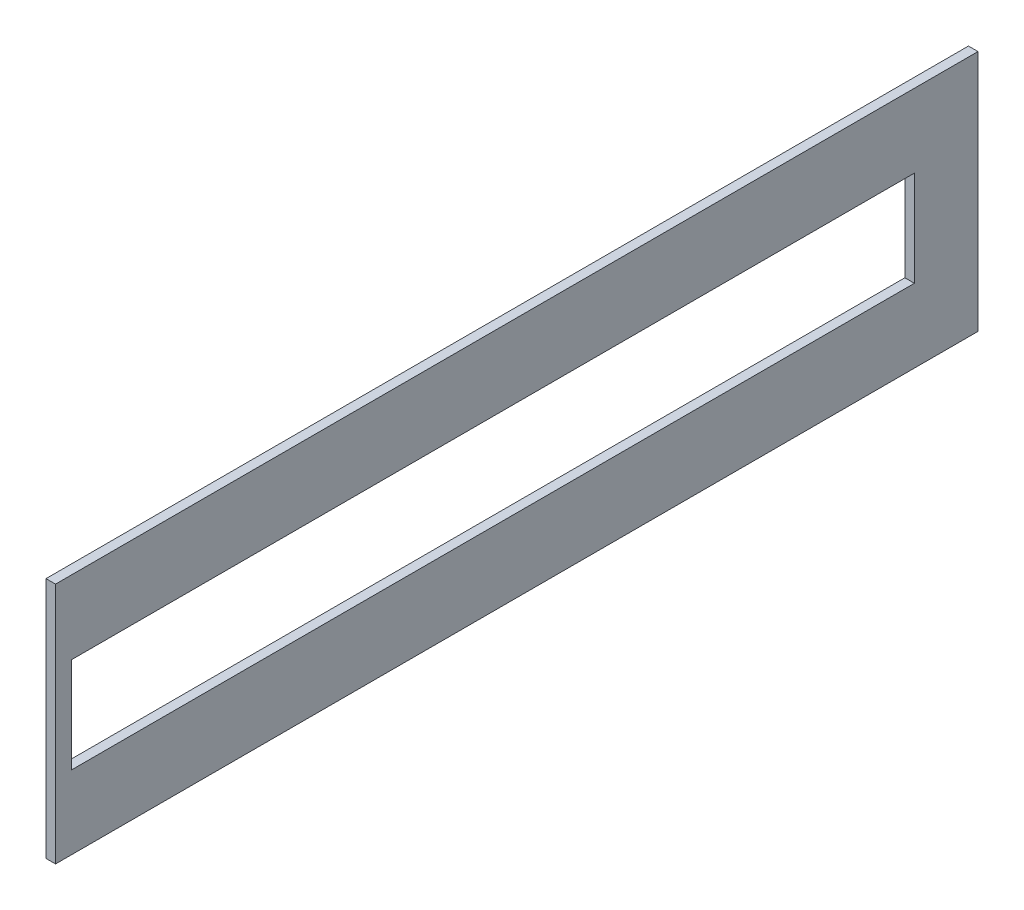
SolidWorks part; units mm, degrees
ref_plane "Front Plane" through (0, 0, 0) normal (0, 0, 1) x (1, 0, 0)
ref_plane "Top Plane" through (0, 0, 0) normal (0, 1, 0) x (1, 0, 0)
ref_plane "Right Plane" through (0, 0, 0) normal (1, 0, 0) x (0, 0, -1)
sketch "Sketch1" plane through (0, 0, 0) normal (1, 0, 0) x (0, 0, -1)
  line L1 (-145, -38.1) -> (145, -38.1)
  line L2 (-145, -38.1) -> (-145, 38.1)
  line L3 (-145, 38.1) -> (145, 38.1)
  line L4 (145, -38.1) -> (145, 38.1)
  line L5 (-145, -38.1) -> (145, 38.1) construction
  line L6 (-145, 38.1) -> (145, -38.1) construction
  point P0 (0, 0)
  dimension "D1" = 76.2
  dimension "D2" = 290
extrude "Boss-Extrude1" add sketch "Sketch1" along normal blind 3
sketch "Sketch2" plane through (3, 0, 0) normal (1, 0, 0) x (0, 0, -1)
  line L0 (25, -12.7) -> (25, 12.7)
  line L5 (25, 12.7) -> (-105, 12.7)
  line L6 (-105, 12.7) -> (-105, -12.7)
  line L7 (-105, -12.7) -> (25, -12.7)
  line L8 (-145, 38.1) -> (-145, -38.1) construction
  dimension "D1" = 25.4
  dimension "D2" = 40
  dimension "D3" = 130
sketch "Sketch3" plane through (3, 0, 0) normal (1, 0, 0) x (0, 0, -1)
  line L0 (-140, 15) -> (125, 15)
  line L1 (125, 15) -> (125, -15)
  line L2 (125, -15) -> (-140, -15)
  line L3 (-140, -15) -> (-140, 15)
  line L4 (-145, 38.1) -> (-145, -38.1) construction
  line L5 (145, -38.1) -> (145, 38.1) construction
  point P9 (-140, 0)
  dimension "D1" = 5
  dimension "D2" = 20
  dimension "D3" = 30
extrude "Cut-Extrude1" cut sketch "Sketch3" against normal through all
